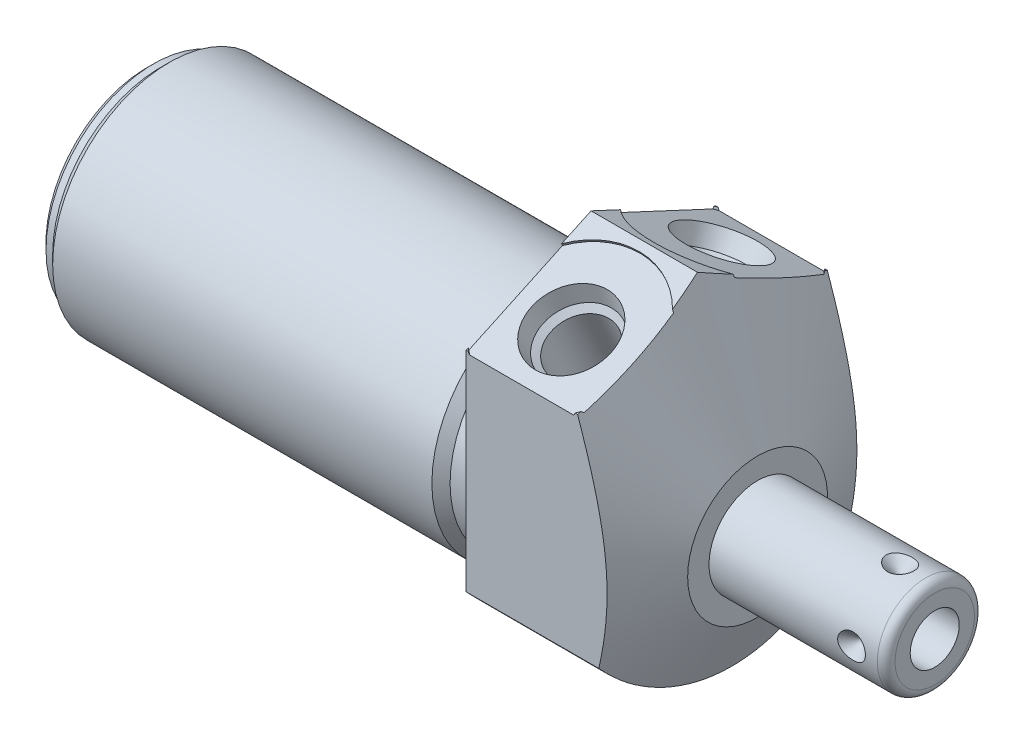
SolidWorks part; units mm, degrees
material "Alloy Steel"
ref_plane "Front Plane" through (0, 0, 0) normal (0, 0, 1) x (1, 0, 0)
ref_plane "Top Plane" through (0, 0, 0) normal (0, 1, 0) x (1, 0, 0)
ref_plane "Right Plane" through (0, 0, 0) normal (1, 0, 0) x (0, 0, -1)
ref_plane "Plane1" through (0, 0, 0) normal (1, 0, 0) x (0, 0, -1)
sketch "Sketch1" plane through (0, 0, 0) normal (1, 0, 0) x (0, 0, -1)
  circle A0 centre (0, 0) radius 19.05
  dimension "D1" = 38.1
extrude "Extrude1" add sketch "Sketch1" along normal blind 19.05 and the other way blind 50.8
ref_plane "Plane2" through (0, 0, 0) normal (1, 0, 0) x (0, 0, -1)
sketch "Sketch2" plane through (0, 0, 0) normal (1, 0, 0) x (0, 0, -1)
  line L0 (-14.6964, -4.7498) -> (14.6964, -4.7498) construction
  circle A0 centre (0, -4.7498) radius 13.3604
  circle A1 centre (0, 0) radius 19.05 construction
  circle A2 centre (0, 0) radius 19.05
  dimension "D1" = 26.7208
  dimension "D2" = 4.7498
extrude "Cut-Extrude1" cut sketch "Sketch2" against normal up to next
ref_plane "Plane4" through (0, 0, 0) normal (-1, 0, 0) x (0, 0, 1)
sketch "Sketch4" plane through (0, 0, 0) normal (-1, 0, 0) x (0, 0, 1)
  line L0 (14.2875, -12.6004) -> (14.2875, 11.3448)
  line L1 (14.2875, 11.3448) -> (0, 18.0071)
  line L2 (-14.2875, -12.6004) -> (-14.2875, 11.3448)
  line L3 (-14.2875, 11.3448) -> (0, 18.0071)
  line L4 (0, -20.9029) -> (0, 19.86) construction
  circle A0 centre (0, 0) radius 19.05 construction
  arc A1 (14.2875, -12.6004) -> (-14.2875, -12.6004) centre (0, 0) ccw
  dimension "D1" = 28.575
  dimension "D2" = 65
  dimension "D3" = 11.3448
extrude "Cut-Extrude3" cut sketch "Sketch4" against normal up to next
ref_plane "Plane6" through (0, 0, 0) normal (0, 0, 1) x (1, 0, 0)
sketch "Sketch6" plane through (0, 0, 0) normal (0, 0, 1) x (1, 0, 0)
  line L0 (12.1692, 18.0071) -> (19.05, 3.2512)
  line L1 (1.9872, -4.7498) -> (19.8625, -4.7498) construction
  line L2 (-50.8, -4.7498) -> (0, -4.7498) construction
  line L3 (19.05, 18.0071) -> (19.05, 11.3448) construction
  line L4 (19.05, 3.2512) -> (19.05, 18.0071)
  line L5 (19.05, 18.0071) -> (12.1692, 18.0071)
  line L6 (19.05, 18.0071) -> (0, 18.0071) construction
  dimension "D1" = 8.001
  dimension "D2" = 25
revolve "Cut-Revolve2" cut sketch "Sketch6" angle 360 about L1
ref_plane "Plane7" through (6.35, 13.7124, 8.6091) normal (1, 0, 0) x (0, 0.4226, -0.9063)
sketch "S2D0002" plane through (6.35, 13.7124, 8.6091) normal (1, 0, 0) x (0, 0.4226, -0.9063)
  line L0 (0, 0) -> (4.5466, 0)
  line L1 (4.5466, 0) -> (4.1066, -2.0701)
  line L2 (4.1066, -2.0701) -> (3.4544, -2.7223)
  line L3 (3.4544, -2.7223) -> (3.4544, -12.192)
  line L4 (3.4544, -12.192) -> (0, -12.192)
  line L5 (0, -12.192) -> (0, 0)
  line L6 (0, -12.8016) -> (0, 0.6096) construction
  dimension "D1" = 12.192
revolve "Cut-Revolve3" cut sketch "S2D0002" angle 360 about L6
ref_plane "Plane8" through (6.35, 13.7124, -8.6091) normal (1, 0, 0) x (0, -0.4226, -0.9063)
sketch "Sketch19" plane through (0, 14.791, 6.8971) normal (0, 0.9063, 0.4226) x (1, 0, 0)
  circle A0 centre (6.35, -2.0074) radius 8.6614
  dimension "D1" = 17.3228
extrude "Cut-Extrude4" cut sketch "Sketch19" against normal blind 0.254
sketch "Sketch8" plane through (6.35, 13.7124, -8.6091) normal (1, 0, 0) x (0, -0.4226, -0.9063)
  line L0 (0, 0) -> (4.5466, 0)
  line L1 (4.5466, 0) -> (4.1066, -2.0701)
  line L2 (4.1066, -2.0701) -> (3.4544, -2.7223)
  line L3 (3.4544, -2.7223) -> (3.4544, -12.192)
  line L4 (3.4544, -12.192) -> (0, -12.192)
  line L5 (0, -12.192) -> (0, 0)
  line L6 (0, -12.8016) -> (0, 0.6096) construction
  dimension "D1" = 12.192
revolve "Cut-Revolve4" cut sketch "Sketch8" angle 360 about L6
sketch "Sketch20" plane through (0, 14.791, -6.8971) normal (0, 0.9063, -0.4226) x (1, 0, 0)
  circle A0 centre (6.35, 2.0074) radius 8.6614
  dimension "D1" = 17.3228
extrude "Cut-Extrude5" cut sketch "Sketch20" against normal blind 0.254
ref_plane "Plane10" through (0, 0, 0) normal (0, 0, 1) x (1, 0, 0)
sketch "Sketch10" plane through (0, 0, 0) normal (0, 0, 1) x (1, 0, 0)
  line L0 (0, 8.6106) -> (0, 7.5692)
  line L1 (0, 7.5692) -> (-3.81, 7.5692)
  line L2 (-3.81, 7.5692) -> (-4.8514, 8.6106)
  line L3 (-5.094, -4.7498) -> (0.2426, -4.7498) construction
  line L4 (0, 8.6106) -> (-4.8514, 8.6106)
  line L5 (-50.8, -4.7498) -> (0, -4.7498) construction
  line L6 (0, 8.6106) -> (-50.8, 8.6106) construction
  line L7 (0, 11.3448) -> (0, -12.6004) construction
  dimension "D1" = 24.638
  dimension "D2" = 3.81
  dimension "D3" = 45
revolve "Cut-Revolve6" cut sketch "Sketch10" angle 360 about L3
ref_plane "Plane12" through (0, 0, 0) normal (0, 0, 1) x (1, 0, 0)
sketch "Sketch12" plane through (0, 0, 0) normal (0, 0, 1) x (1, 0, 0)
  line L0 (-50.8, 8.6106) -> (-50.8, 7.5692)
  line L1 (-50.8, 7.5692) -> (-49.276, 7.5692)
  line L2 (-49.276, 7.5692) -> (-48.2346, 8.6106)
  line L3 (-50.9283, -4.7498) -> (-48.1063, -4.7498) construction
  line L4 (-50.8, 8.6106) -> (-48.2346, 8.6106)
  line L5 (-50.8, -4.7498) -> (-4.8514, -4.7498) construction
  line L6 (-4.8514, 8.6106) -> (-50.8, 8.6106) construction
  line L7 (-50.8, 8.6106) -> (-50.8, -18.1102) construction
  dimension "D1" = 24.638
  dimension "D2" = 1.524
  dimension "D3" = 45
revolve "Cut-Revolve8" cut sketch "Sketch12" angle 360 about L3
chamfer "Chamfer1" distance 0.762 angle 45 1 edges at (-50.8, -4.7498, 12.319)
ref_plane "Plane13" through (0, 0, 0) normal (0, 0, 1) x (0, -1, 0)
sketch "Sketch13" plane through (0, 0, 0) normal (0, 0, 1) x (0, -1, 0)
  line L0 (4.7498, 19.05) -> (4.7498, 39.3192)
  line L1 (4.7498, 39.3192) -> (9.2901, 39.3192)
  line L2 (10.306, 38.3032) -> (10.306, 19.05)
  line L3 (10.306, 19.05) -> (4.7498, 19.05)
  line L4 (4.7498, 18.0365) -> (4.7498, 40.3327) construction
  line L5 (4.7498, -48.2346) -> (4.7498, -4.8514) construction
  line L6 (12.7508, 19.05) -> (-3.2512, 19.05) construction
  line L7 (-11.3448, 0) -> (12.6004, 0) construction
  arc A0 (10.306, 38.3032) -> (9.2901, 39.3192) centre (9.2901, 38.3032) ccw
  dimension "D2" = 1.016
  dimension "D1" = 39.3192
  dimension "D3" = 11.1125
revolve "Revolve1" add sketch "Sketch13" angle 360 about L4
ref_plane "Plane14" through (39.3192, -7.5565, 0) normal (0, 0, 1) x (0, -1, 0)
sketch "S2D0001" plane through (39.3192, -7.5565, 0) normal (0, 0, 1) x (0, -1, 0)
  line L0 (0, 0) -> (0, -10.16)
  line L1 (0, -10.16) -> (-2.8067, -11.8464)
  line L2 (0, 0) -> (-2.8067, 0)
  line L3 (-2.8067, 0) -> (-2.8067, -11.8464)
  line L4 (-2.8067, -12.4388) -> (-2.8067, 0.5923) construction
  line L5 (-2.8067, -1.016) -> (-2.8067, -20.2692) construction
  line L6 (1.7336, 0) -> (-7.347, 0) construction
  dimension "D1" = 5.6134
  dimension "D2" = 59
  dimension "D3" = 10.16
revolve "Cut-Revolve9" cut sketch "S2D0001" angle 360 about L4
ref_plane "Plane16" through (35.3568, -10.306, 0) normal (0, 0, 1) x (-1, 0, 0)
ref_plane "Plane17" through (0, 0, 0) normal (0, 0, 1) x (-1, 0, 0)
sketch "Sketch16" plane through (35.3568, 2.1976, 0) normal (0, 0, -1) x (-1, 0, 0)
  line L0 (0, -1.3912) -> (1.5875, -1.3912)
  line L1 (1.5875, -1.3912) -> (0, -2.9787)
  line L2 (0, -1.3912) -> (0, -2.9787)
  line L3 (0, -3.4788) -> (0, 0.0794) construction
  line L4 (-3.9624, -2.4072) -> (-3.9624, -11.4877) construction
  line L5 (16.3068, -1.3912) -> (-2.9464, -1.3912) construction
  dimension "D1" = 3.9624
  dimension "D2" = 3.175
  dimension "D3" = 45
revolve "Cut-Revolve10" cut sketch "Sketch16" angle 360 about L3
pattern_circular "CirPattern1" count 4 over 360 about axis through (18.0365, -4.7498, 0) along (-1, 0, 0) of "Cut-Revolve10"
